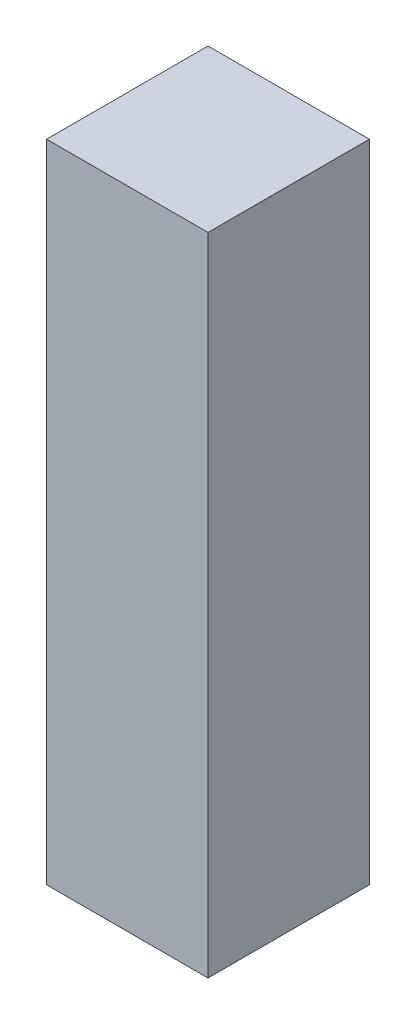
SolidWorks part; units mm, degrees
material "Oak"
ref_plane "Front Plane" through (0, 0, 0) normal (0, 0, 1) x (1, 0, 0)
ref_plane "Top Plane" through (0, 0, 0) normal (0, 1, 0) x (1, 0, 0)
ref_plane "Right Plane" through (0, 0, 0) normal (1, 0, 0) x (0, 0, -1)
sketch "Sketch1" plane through (0, 0, 0) normal (0, 1, 0) x (1, 0, 0)
  line L1 (-9.525, -9.525) -> (9.525, -9.525)
  line L2 (-9.525, -9.525) -> (-9.525, 9.525)
  line L3 (-9.525, 9.525) -> (9.525, 9.525)
  line L4 (9.525, -9.525) -> (9.525, 9.525)
  line L5 (-9.525, -9.525) -> (9.525, 9.525) construction
  line L6 (-9.525, 9.525) -> (9.525, -9.525) construction
  point P0 (0, 0)
  dimension "D1" = 19.05
extrude "Boss-Extrude1" add sketch "Sketch1" along normal blind 76.2
